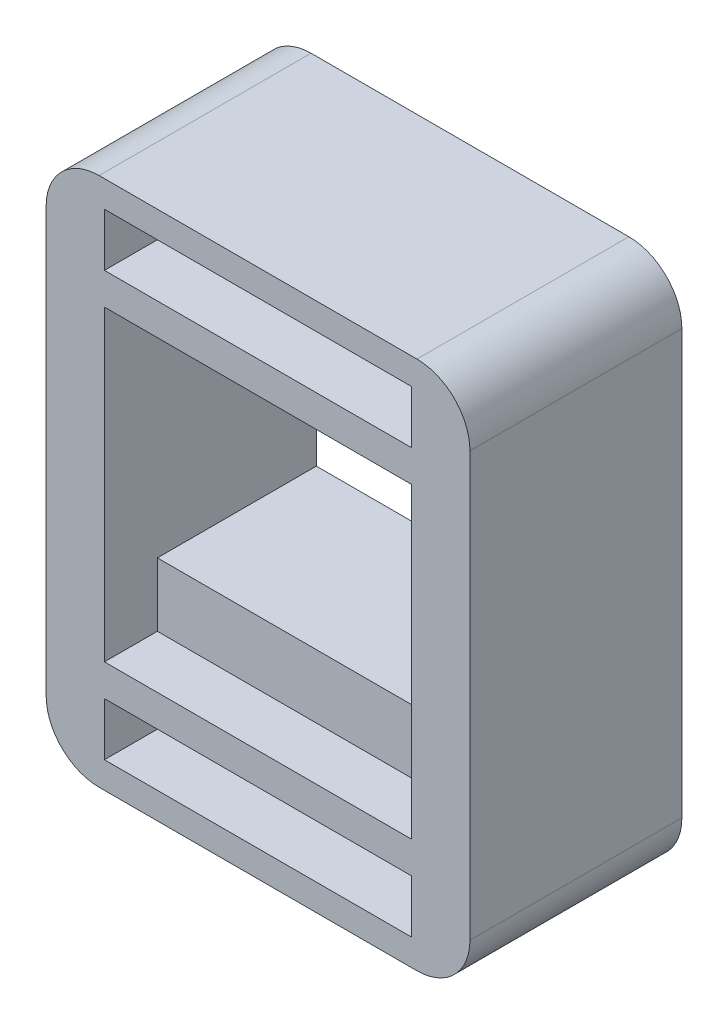
SolidWorks part; units mm, degrees
ref_plane "Front Plane" through (0, 0, 0) normal (0, 0, 1) x (1, 0, 0)
ref_plane "Top Plane" through (0, 0, 0) normal (0, 1, 0) x (1, 0, 0)
ref_plane "Right Plane" through (0, 0, 0) normal (1, 0, 0) x (0, 0, -1)
sketch "Sketch2" plane through (0, 0, 0) normal (0, 0, 1) x (1, 0, 0)
  line L0 (-5.5, 14.5) -> (38.2901, 14.5) construction
  line L1 (0, 0) -> (29, 0)
  line L2 (0, 0) -> (0, 29)
  line L3 (0, 29) -> (29, 29)
  line L4 (29, 0) -> (29, 29)
  line L5 (-0.5, -10.5) -> (29.5, -10.5)
  line L6 (-5.5, -5.5) -> (-5.5, 34.5)
  line L7 (-0.5, 39.5) -> (29.5, 39.5)
  line L8 (34.5, -5.5) -> (34.5, 34.5)
  line L9 (0, 37) -> (29, 37)
  line L10 (0, 37) -> (0, 32)
  line L11 (0, 32) -> (29, 32)
  line L12 (29, 37) -> (29, 32)
  line L13 (0, -3) -> (29, -3)
  line L14 (29, -8) -> (29, -3)
  line L15 (0, -8) -> (29, -8)
  line L16 (0, -8) -> (0, -3)
  line L30 (0, 0) -> (29, 0)
  line L31 (0, 0) -> (0, 6)
  line L32 (0, 6) -> (29, 6)
  line L33 (29, 0) -> (29, 6)
  line L34 (0, 29) -> (8, 29)
  line L35 (0, 29) -> (0, 24)
  line L36 (0, 24) -> (8, 24)
  line L37 (8, 29) -> (8, 24)
  line L38 (29, 29) -> (21, 29)
  line L39 (29, 29) -> (29, 24)
  line L40 (29, 24) -> (21, 24)
  line L41 (21, 29) -> (21, 24)
  arc A0 (29.5, -10.5) -> (34.5, -5.5) centre (29.5, -5.5) ccw
  arc A1 (-0.5, -10.5) -> (-5.5, -5.5) centre (-0.5, -5.5) cw
  arc A2 (29.5, 39.5) -> (34.5, 34.5) centre (29.5, 34.5) cw
  arc A3 (-5.5, 34.5) -> (-0.5, 39.5) centre (-0.5, 34.5) cw
  point P9 (14.5, 39.5)
  point P10 (14.5, 29)
  point P11 (0, 14.5)
  point P12 (-5.5, 14.5)
  point P17 (-5.5, -10.5)
  point P20 (34.5, 39.5)
  point P23 (-5.5, 39.5)
  point P28 (14.5, 37)
  dimension "D4" = 5
  dimension "D1" = 50
  dimension "27" = 29
  dimension "D3" = 40
  dimension "D5" = 29
  dimension "D6" = 5
  dimension "D7" = 2.5
  dimension "D8" = 29
  dimension "D21" = 6
  dimension "D22" = 5
  dimension "D23" = 8
  dimension "D24" = 5
  dimension "D25" = 8
extrude "Boss-Extrude2" add sketch "Sketch2" along normal blind 20 contours L6 L0 L2 L3 L4 L8 A2 L7 A3 L9 L12 L11 L10 | L0 L6 A1 L5 A0 L8 L4 L1 L2 L15 L16 L13 L14 | L37 L3 L2 L36 | L3 L41 L40 L4 | L31 L30 L33 L32
sketch "Sketch3" plane through (0, 0, 20) normal (0, 0, 1) x (1, 0, 0)
  line L1 (8, 24) -> (0, 24)
  line L2 (8, 24) -> (8, 29)
  line L3 (8, 29) -> (0, 29)
  line L4 (0, 24) -> (0, 29)
  line L5 (21, 24) -> (29, 24)
  line L6 (21, 24) -> (21, 29)
  line L7 (21, 29) -> (29, 29)
  line L8 (29, 24) -> (29, 29)
  line L9 (0, 0) -> (29, 0)
  line L10 (0, 0) -> (0, 6)
  line L11 (0, 6) -> (29, 6)
  line L12 (29, 0) -> (29, 6)
  dimension "D1" = 8
  dimension "D2" = 5
  dimension "D3" = 8
  dimension "D4" = 5
extrude "Cut-Extrude1" cut sketch "Sketch3" against normal blind 5
